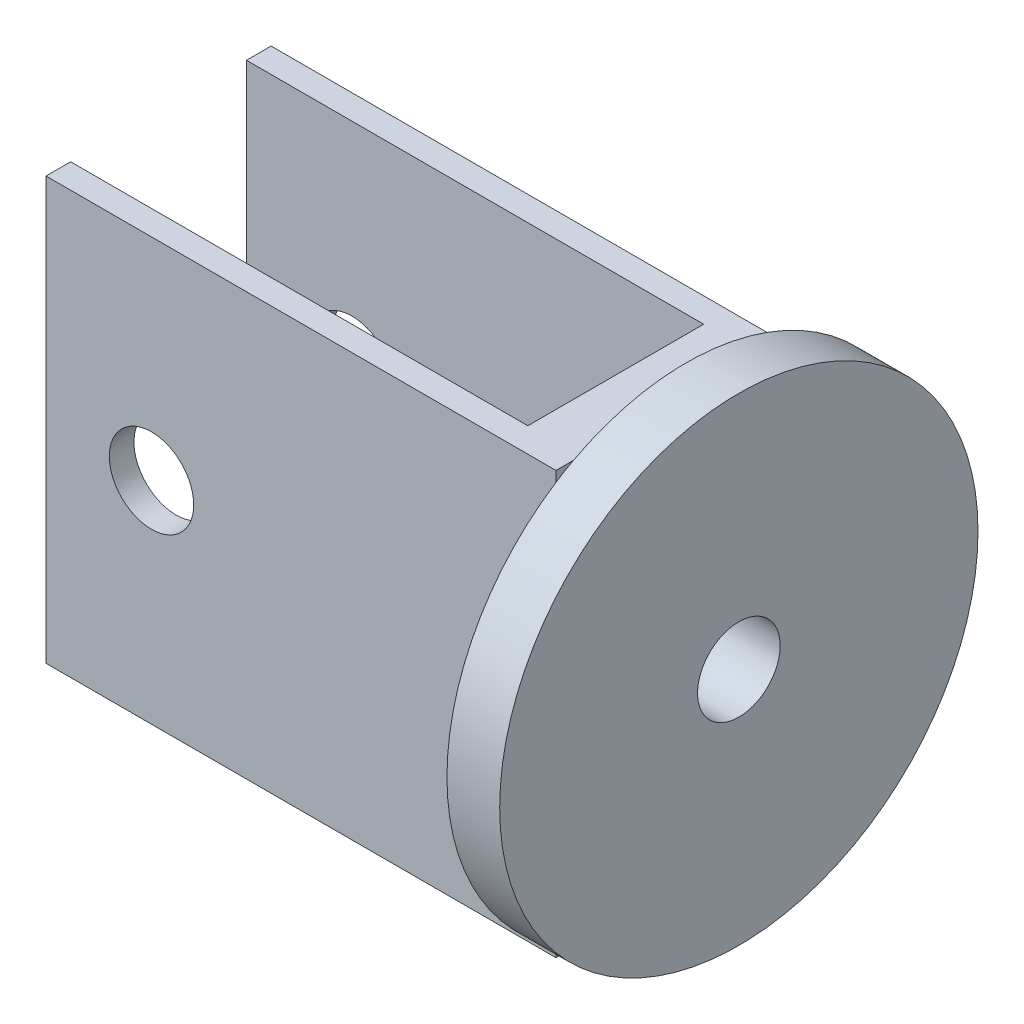
SolidWorks part; units mm, degrees
ref_plane "Ön Düzlem" through (0, 0, 0) normal (0, 0, 1) x (1, 0, 0)
ref_plane "Üst Düzlem" through (0, 0, 0) normal (0, 1, 0) x (1, 0, 0)
ref_plane "Sağ Düzlem" through (0, 0, 0) normal (1, 0, 0) x (0, 0, -1)
sketch "Sketch1" plane through (0, 0, 0) normal (0, 1, 0) x (1, 0, 0)
  line L0 (0, -20) -> (0, -6)
  line L1 (0, -6) -> (290, -6)
  line L2 (290, -6) -> (290, -134)
  line L3 (290, -134) -> (0, -134)
  line L4 (0, -134) -> (0, -120)
  line L5 (0, -120) -> (260, -120)
  line L6 (260, -120) -> (260, -20)
  line L7 (260, -20) -> (0, -20)
  line L8 (0, -20) -> (0, -6) construction
  dimension "D1" = 260
  dimension "D2" = 30
  dimension "D3" = 14
  dimension "D4" = 14
  dimension "D5" = 100
  dimension "D6" = 290
extrude "Boss-Extrude1" add sketch "Sketch1" along normal blind 240
sketch "Sketch5" plane through (290, 0, 0) normal (1, 0, 0) x (0, 0, -1)
  line L0 (-60, 0) -> (-60, 240) construction
  circle A0 centre (-60, 120) radius 136
extrude "Boss-Extrude2" add sketch "Sketch5" along normal blind 30
sketch "Çizim1" plane through (320, 0, 0) normal (1, 0, 0) x (0, 0, -1)
  circle A0 centre (-60, 120) radius 23.5
  dimension "D1" = 47
extrude "Kes-Ekstrüzyon1" cut sketch "Çizim1" against normal blind 80
sketch "Çizim2" plane through (260, 0, 0) normal (-1, 0, 0) x (0, 0, 1)
  circle A0 centre (60, 120) radius 10
  circle A1 centre (60, 120) radius 25
  dimension "D1" = 20
  dimension "D2" = 50
extrude "Yükseklik-Ekstrüzyon1" add sketch "Çizim2" against normal blind 10
scale "Scale1" scale about centroid uniform scaling yes scale factor 0.25
sketch "Sketch6" plane through (0, 0, 83.1311) normal (0, 0, 1) x (1, 0, 0)
  line L0 (171.0674, 150) -> (171.0674, 90) construction
  circle A0 centre (186.0674, 120) radius 6
  point P4 (171.0674, 120)
  dimension "D1" = 15
extrude "Cut-Extrude1" cut sketch "Sketch6" against normal blind 200
